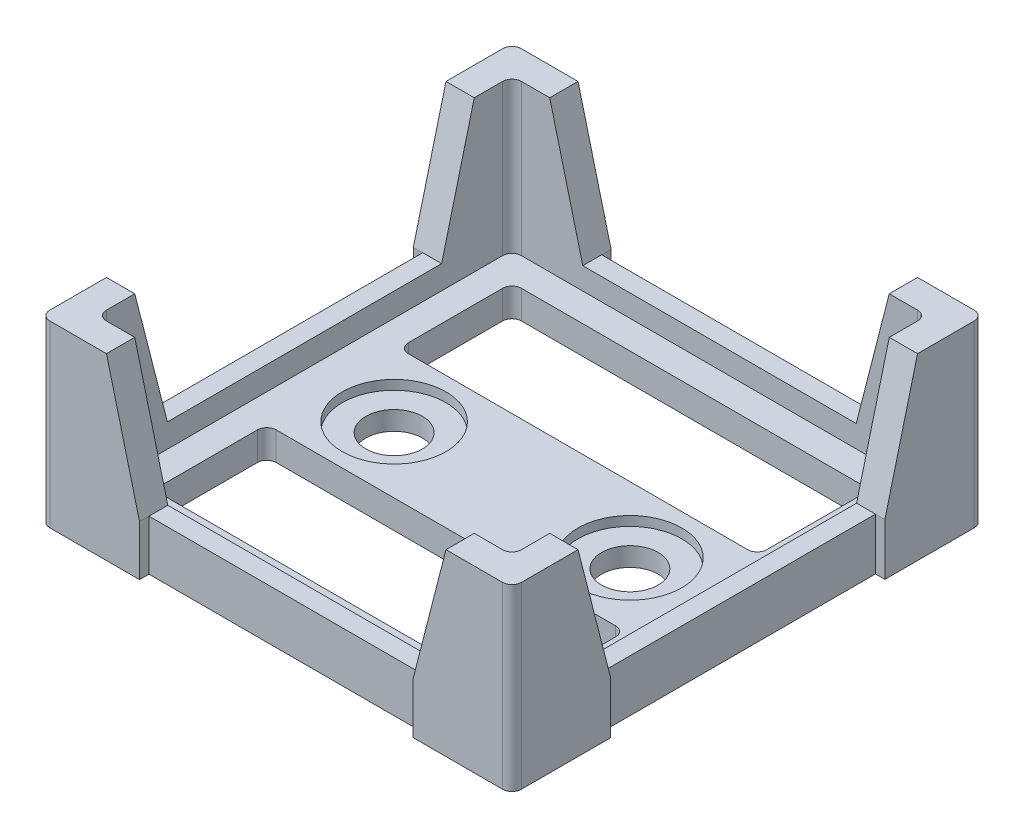
SolidWorks part; units mm, degrees
ref_plane "Front Plane" through (0, 0, 0) normal (0, 0, 1) x (1, 0, 0)
ref_plane "Top Plane" through (0, 0, 0) normal (0, 1, 0) x (1, 0, 0)
ref_plane "Right Plane" through (0, 0, 0) normal (1, 0, 0) x (0, 0, -1)
sketch "Sketch1" plane through (0, 0, 0) normal (0, 1, 0) x (1, 0, 0)
  line L0 (0, 0) -> (25, 0) construction
  line L1 (-25, 25) -> (25, 25)
  line L2 (-25, 25) -> (-25, -25)
  line L3 (-25, -25) -> (25, -25)
  line L4 (25, 25) -> (25, -25)
  line L5 (0, 0) -> (0, 25) construction
  dimension "D1" = 50
extrude "Boss-Extrude1" add sketch "Sketch1" along normal blind 19
sketch "Sketch2" plane through (0, 19, 0) normal (0, 1, 0) x (1, 0, 0)
  line L0 (0, 0) -> (0, 22) construction
  line L1 (-22, 22) -> (22, 22)
  line L2 (-22, 22) -> (-22, -22)
  line L3 (-22, -22) -> (22, -22)
  line L4 (22, 22) -> (22, -22)
  line L5 (0, 0) -> (22, 0) construction
  dimension "D1" = 44
extrude "Cut-Extrude1" cut sketch "Sketch2" against normal blind 16
sketch "Sketch3" plane through (0, 3, 0) normal (0, 1, 0) x (1, 0, 0)
  line L0 (0, 0) -> (0, 27.2561) construction
  point P0 (-12.5, 0)
  point P1 (12.5, 0)
  dimension "D1" = 25
hole_wizard "CBORE for M6 SHCS1" positions "3DSketch1" profile "Sketch5" counterbore size "M6" standard "ANSI Metric" end condition through all
sketch3d "3DSketch1"
  point P0 (-12.5, 3, 0)
  point P3 (12.5, 3, 0)
sketch "Sketch5" plane through (-12.5, 3, 0) normal (1, 0, 0) x (0, 0, 1)
  line L0 (0, 0) -> (0, 3)
  line L1 (0, 3) -> (3, 3)
  line L3 (3, 3) -> (3, 1)
  line L4 (3, 1) -> (5.5, 1)
  line L5 (5.5, 1) -> (5.5, 0)
  line L7 (5.5, 0) -> (0, 0)
  line L11 (0, -6.35) -> (0, 107.95) construction
  dimension "Thru Hole Dia." = 6
  dimension "Thru Hole Depth" = 3
  dimension "C'Bore Dia." = 11
  dimension "C'Bore Depth" = 1
sketch "Sketch6" plane through (0, 3, 0) normal (0, 1, 0) x (1, 0, 0)
  line L0 (0, 0) -> (26.633, 0) construction
  line L1 (-19, -19) -> (19, -19)
  line L2 (-19, -19) -> (-19, -7)
  line L3 (-19, -7) -> (19, -7)
  line L4 (19, -19) -> (19, -7)
  line L5 (-19, 19) -> (19, 19)
  line L6 (19, 19) -> (19, 7)
  line L7 (-19, 19) -> (-19, 7)
  line L8 (-19, 7) -> (19, 7)
  line L9 (0, 0) -> (0, 29.6458) construction
  line L10 (-22, 22) -> (-22, -22) construction
  line L11 (-22, -22) -> (22, -22) construction
  circle A0 centre (-12.5, 0) radius 5.5 construction
  dimension "D1" = 3
  dimension "D2" = 3
  dimension "D3" = 7
extrude "Cut-Extrude2" cut sketch "Sketch6" against normal blind 16
fillet "Fillet1" radius 1 12 edges at (-22, 11, 22) (19, 1.5, 7) (22, 11, 22) (19, 1.5, 19) (19, 1.5, -7) (19, 1.5, -19) (22, 11, -22) (-22, 11, -22) (-19, 1.5, -19) (-19, 1.5, 7) (-19, 1.5, 19) (-19, 1.5, -7)
fillet "Fillet3" radius 1 4 edges at (-25, 9.5, -25) (25, 9.5, -25) (25, 9.5, 25) (-25, 9.5, 25)
sketch "Sketch7" plane through (25, 0, 0) normal (1, 0, 0) x (0, 0, -1)
  line L0 (-24, 0) -> (24, 0) construction
  line L1 (-24, 0) -> (24, 0) construction
  line L3 (0, 0) -> (0, 5.5) construction
  line L5 (14.5388, 5.5) -> (-14.5388, 5.5)
  line L7 (0, 0) -> (0, 19) construction
  line L8 (-24, 19) -> (24, 19) construction
  line L9 (-18, 19) -> (18, 19)
  line L10 (-18, 19) -> (-14.5388, 5.5)
  line L11 (14.5388, 5.5) -> (18, 19)
  point P6 (0, 0)
  dimension "D1" = 36
  dimension "D2" = 5.5
  dimension "D3" = 104.38
extrude "Cut-Extrude3" cut sketch "Sketch7" against normal through all
sketch "Sketch8" plane through (0, 0, 25) normal (0, 0, 1) x (1, 0, 0)
  line L0 (0, 0) -> (0, 19) construction
  line L1 (-24, 19) -> (24, 19) construction
  line L2 (-18, 19) -> (18, 19)
  line L3 (-14.4955, 5.331) -> (14.4955, 5.331)
  line L4 (-18, 19) -> (-14.4955, 5.331)
  line L5 (18, 19) -> (14.4955, 5.331)
  point P10 (0, 5.331)
  dimension "D1" = 36
  dimension "D2" = 104.38
extrude "Cut-Extrude4" cut sketch "Sketch8" against normal through all contours L4 L3 L5 L2
sketch "Sketch9" plane through (0, 5.5, 0) normal (0, 1, 0) x (1, 0, 0)
  line L0 (25, -14.5388) -> (25, 14.5388) construction
  line L1 (25, -14.5388) -> (25, 14.5388)
  line L2 (25, -14.5388) -> (24, -14.5388)
  line L4 (22, -14.5388) -> (25, -14.5388) construction
  line L5 (24, -14.5388) -> (24, 14.5388)
  line L6 (22, 14.5388) -> (25, 14.5388) construction
  line L7 (24, 14.5388) -> (25, 14.5388)
  dimension "D1" = 1
extrude "Cut-Extrude5" cut sketch "Sketch9" against normal blind 10 contours L1 L7 L5 L2
sketch "Sketch10" plane through (0, 5.331, 0) normal (0, 1, 0) x (1, 0, 0)
  line L0 (-14.4955, -25) -> (14.4955, -25) construction
  line L1 (-14.4955, -25) -> (14.4955, -25)
  line L2 (-14.4955, -25) -> (-14.4955, -24)
  line L3 (-14.4955, -22) -> (-14.4955, -25) construction
  line L4 (-14.4955, -24) -> (14.4955, -24)
  line L5 (14.4955, -22) -> (14.4955, -25) construction
  line L6 (14.4955, -24) -> (14.4955, -25)
  dimension "D1" = 1
extrude "Cut-Extrude6" cut sketch "Sketch10" against normal blind 10
sketch "Sketch11" plane through (0, 5.331, 0) normal (0, 1, 0) x (1, 0, 0)
  line L0 (-14.4955, 25) -> (14.4955, 25) construction
  line L1 (-14.4955, 25) -> (14.4955, 25)
  line L2 (14.4955, 25) -> (14.4955, 24)
  line L3 (14.4955, 25) -> (14.4955, 22) construction
  line L4 (14.4955, 24) -> (-14.4955, 24)
  line L5 (-14.4955, 25) -> (-14.4955, 22) construction
  line L6 (-14.4955, 25) -> (-14.4955, 24)
  dimension "D1" = 1
extrude "Cut-Extrude7" cut sketch "Sketch11" against normal blind 10
sketch "Sketch12" plane through (0, 5.5, 0) normal (0, 1, 0) x (1, 0, 0)
  line L0 (-25, -14.5388) -> (-25, 14.5388) construction
  line L1 (-25, -14.5388) -> (-25, 14.5388)
  line L2 (-25, 14.5388) -> (-24, 14.5388)
  line L3 (-25, 14.5388) -> (-22, 14.5388) construction
  line L4 (-24, 14.5388) -> (-24, -14.5388)
  line L5 (-25, -14.5388) -> (-22, -14.5388) construction
  line L6 (-25, -14.5388) -> (-24, -14.5388)
  dimension "D1" = 1
extrude "Cut-Extrude8" cut sketch "Sketch12" against normal blind 10
